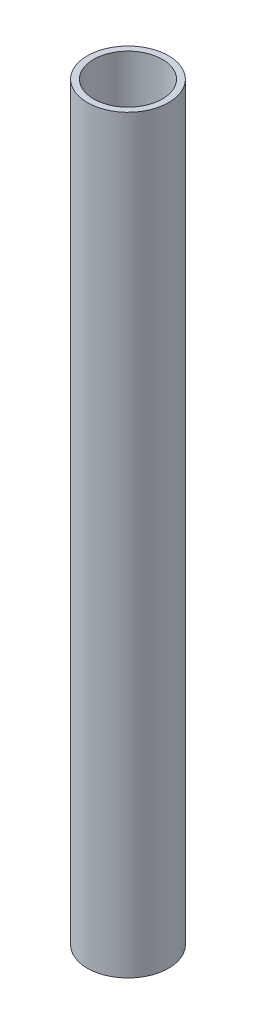
SolidWorks part; units mm, degrees
material "Hexcel AS4C (3000 Filaments)"
ref_plane "Front Plane" through (0, 0, 0) normal (0, 0, 1) x (1, 0, 0)
ref_plane "Top Plane" through (0, 0, 0) normal (0, 1, 0) x (1, 0, 0)
ref_plane "Right Plane" through (0, 0, 0) normal (1, 0, 0) x (0, 0, -1)
sketch "Sketch1" plane through (0, 0, 0) normal (0, 1, 0) x (1, 0, 0)
  circle A0 centre (0, 0) radius 6.5
  circle A1 centre (0, 0) radius 5.5
extrude "Boss-Extrude1" add sketch "Sketch1" along normal blind 120
